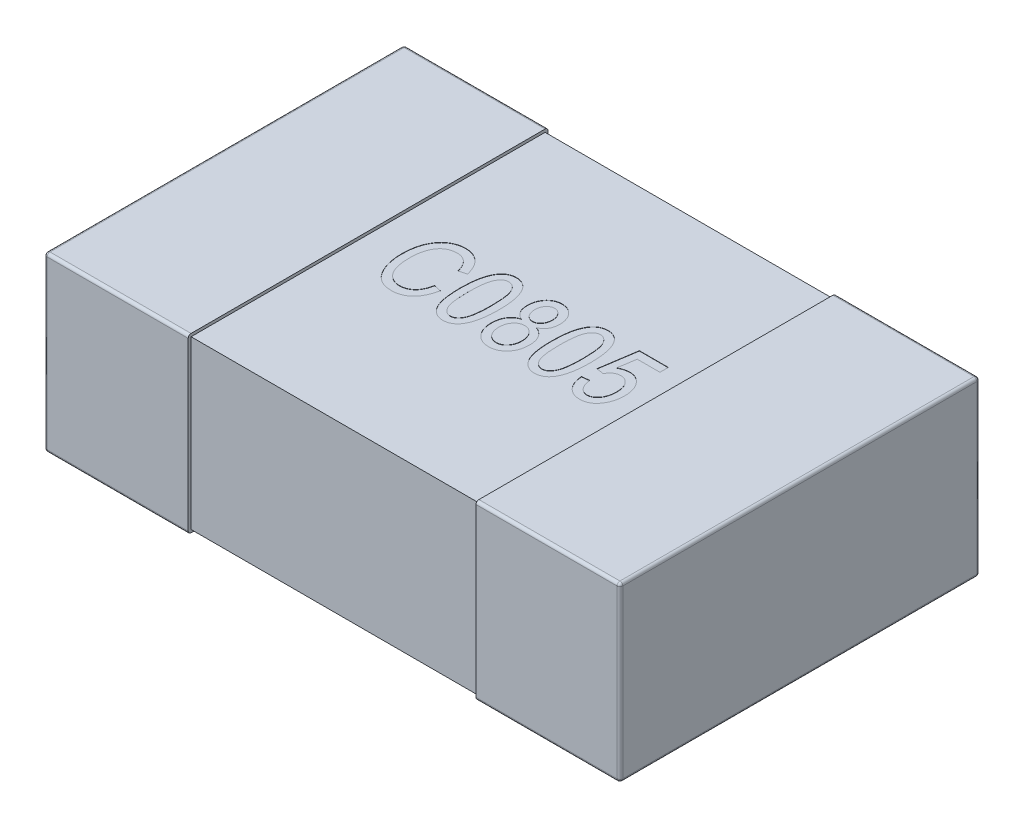
SolidWorks part; units mm, degrees
ref_plane "Front Plane" through (0, 0, 0) normal (0, 0, 1) x (1, 0, 0)
ref_plane "Top Plane" through (0, 0, 0) normal (0, 1, 0) x (1, 0, 0)
ref_plane "Right Plane" through (0, 0, 0) normal (1, 0, 0) x (0, 0, -1)
sketch "Sketch1" plane through (0, 0, 0) normal (0, 1, 0) x (1, 0, 0)
  line L0 (0, 0.15) -> (0, -0.15) construction
  line L1 (-1, 0) -> (0, 0) construction
  line L3 (-1, 0.625) -> (-0.5, 0.625)
  line L4 (-1, 0.625) -> (-1, -0.625)
  line L5 (-1, -0.625) -> (-0.5, -0.625)
  line L6 (-0.5, 0.625) -> (-0.5, -0.625)
  dimension "BANDWIDTH" = 0.5
  dimension "WIDTH" = 1.25
  dimension "LENGTH-HALF" = 1
extrude "THICKNESS" add sketch "Sketch1" along normal blind 0.6
fillet "Fillet1" radius 0.01 8 edges at (-1, 0, 0) (-0.75, 0, -0.625) (-1, 0.3, -0.625) (-0.75, 0, 0.625) (-1, 0.3, 0.625) (-1, 0.6, 0) (-0.75, 0.6, -0.625) (-0.75, 0.6, 0.625)
sketch "Sketch2" plane through (0, 0, 0) normal (1, 0, 0) x (0, 0, -1)
  line L0 (0, 0.6) -> (0, 0) construction
  line L1 (-0.615, 0.59) -> (0.615, 0.59)
  line L2 (-0.615, 0.59) -> (-0.615, 0.01)
  line L3 (-0.615, 0.01) -> (0.615, 0.01)
  line L4 (0.615, 0.59) -> (0.615, 0.01)
  line L5 (-0.615, 0.6) -> (0.615, 0.6) construction
  line L6 (-0.615, 0) -> (0.615, 0) construction
  line L7 (-0.625, 0.3) -> (0.625, 0.3) construction
  line L8 (-0.625, 0.59) -> (-0.625, 0.01) construction
  line L9 (0.625, 0.59) -> (0.625, 0.01) construction
  dimension "D1" = 0.01
  dimension "D2" = 0.01
extrude "Boss-Extrude2" add sketch "Sketch2" against normal up to surface (0.5 mm away) up to face at (-0.5, 0.3, 0)
mirror "Mirror3" about plane through (0, 0, 0) normal (1, 0, 0) of "Boss-Extrude2", "Fillet1", "THICKNESS"
sketch "Sketch3" plane through (0, 0.59, 0) normal (0, 1, 0) x (1, 0, 0)
  line L0 (-0.4, -0.125) -> (0.4, -0.125) construction
  line L1 (0, -0.33) -> (0, 0.33) construction
  line L2 (-0.33, 0) -> (0.33, 0) construction
  text T0 "C0805" font "Arial Narrow" height 0.25
  point P2 (0, -0.125)
  dimension "D1" = 0.8
  dimension "D2" = 0.125
extrude "Cut-Extrude1" cut sketch "Sketch3" against normal blind 0.001
